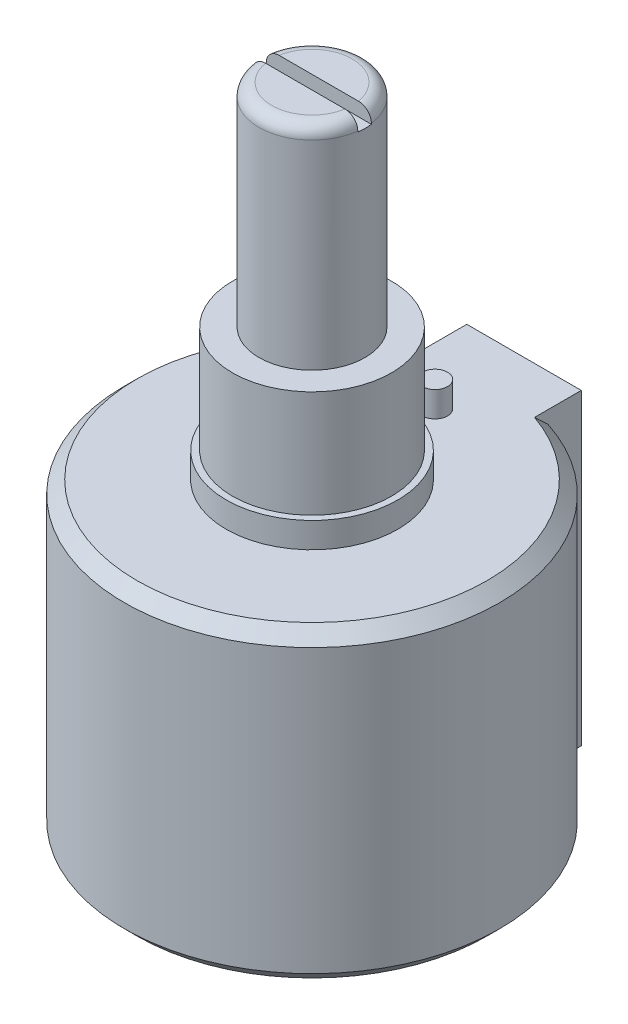
SolidWorks part; units mm, degrees
ref_plane "Front Plane" through (0, 0, 0) normal (0, 0, 1) x (1, 0, 0)
ref_plane "Top Plane" through (0, 0, 0) normal (0, 1, 0) x (1, 0, 0)
ref_plane "Right Plane" through (0, 0, 0) normal (1, 0, 0) x (0, 0, -1)
sketch "Sketch1" plane through (0, 0, 0) normal (0, 1, 0) x (1, 0, 0)
  line L0 (0, 0) -> (0, 12.7) construction
  line L1 (3.429, 12.7) -> (-3.429, 12.7)
  line L2 (-3.429, 12.7) -> (-3.429, 10.7037)
  line L3 (3.429, 12.7) -> (3.429, 10.7037)
  circle A0 centre (0, 0) radius 11.2395 construction
  arc A1 (-3.429, 10.7037) -> (3.429, 10.7037) centre (0, 0) ccw
  dimension "D1" = 22.479
  dimension "D2" = 6.858
  dimension "D3" = 12.7
extrude "Body" add sketch "Sketch1" along normal blind 18.4404
sketch "Sketch3" plane through (0, 18.4404, 0) normal (0, 1, 0) x (1, 0, 0)
  line L0 (0, 0) -> (0, 7.366) construction
  circle A0 centre (0, 0) radius 5.1435
  circle A1 centre (0, 7.366) radius 0.7493
  dimension "D1" = 10.287
  dimension "D2" = 1.4986
  dimension "D3" = 7.366
extrude "Boss-Extrude2" add sketch "Sketch3" along normal blind 1.524
sketch "Sketch4" plane through (0, 19.9644, 0) normal (0, 1, 0) x (1, 0, 0)
  circle A0 centre (0, 0) radius 4.7625
  dimension "D1" = 9.525
extrude "Mount Lug" add sketch "Sketch4" along normal blind 6.4008
cosmetic thread "Cosmetic Thread1" parameters "D2"=9.3472
sketch "Sketch5" plane through (0, 26.3652, 0) normal (0, 1, 0) x (1, 0, 0)
  circle A0 centre (0, 0) radius 3.175
  dimension "D1" = 6.35
extrude "Shaft" add sketch "Sketch5" along normal blind 12.7
fillet "Fillet1" radius 0.762 1 edges at (0, 39.0652, 3.175)
sketch "Sketch6" plane through (0, 0, 0) normal (1, 0, 0) x (0, 0, -1)
  line L0 (2.413, 39.0652) -> (-2.413, 39.0652) construction
  line L1 (-0.4064, 38.2524) -> (0.4064, 38.2524)
  line L2 (-0.4064, 38.2524) -> (-0.4064, 39.878)
  line L3 (-0.4064, 39.878) -> (0.4064, 39.878)
  line L4 (0.4064, 38.2524) -> (0.4064, 39.878)
  line L5 (-0.4064, 38.2524) -> (0.4064, 39.878) construction
  line L6 (-0.4064, 39.878) -> (0.4064, 38.2524) construction
  point P0 (0, 39.0652)
  dimension "D1" = 0.8128
  dimension "D2" = 1.6256
extrude "Adj. slot" cut sketch "Sketch6" against normal through all and the other way through all
chamfer "Chamfer1" distance 0.762 angle 45 2 edges at (0, 18.4404, 11.2395) (0, 0, 11.2395)
